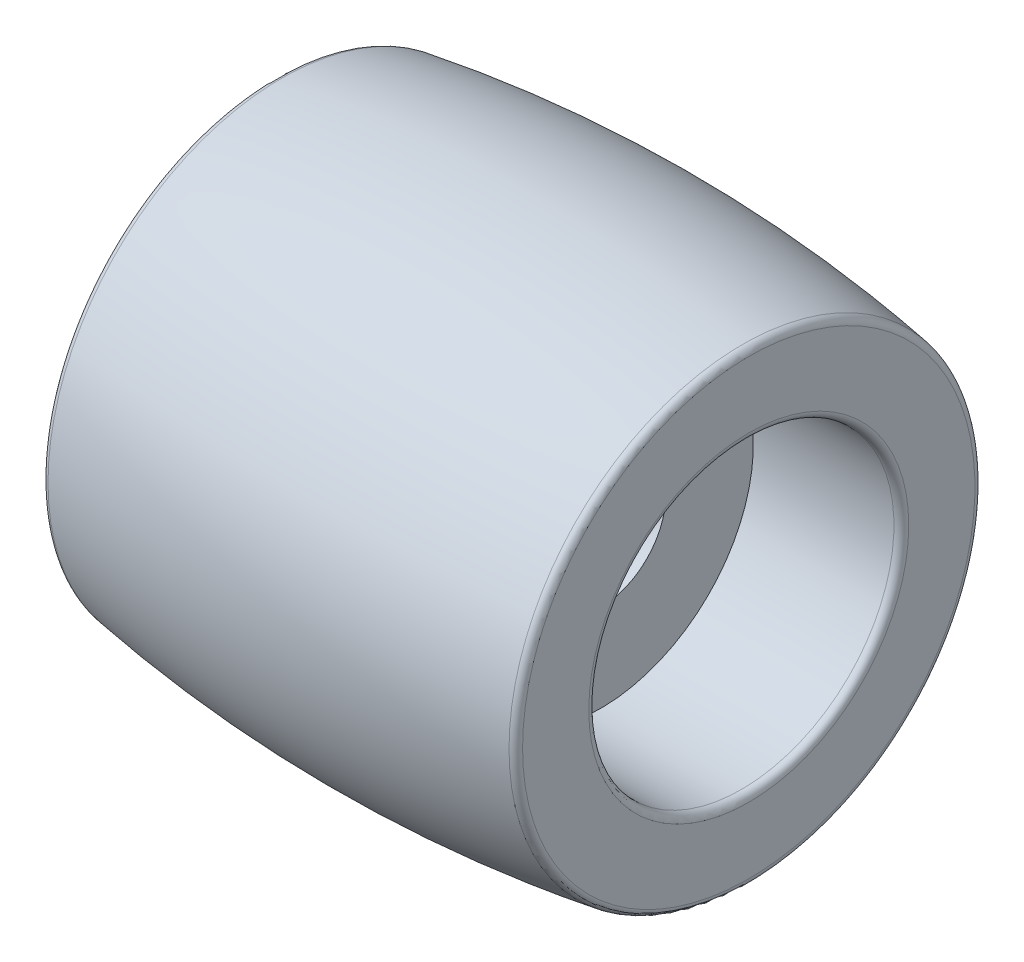
SolidWorks part; units mm, degrees
ref_plane "Front Plane" through (0, 0, 0) normal (0, 0, 1) x (1, 0, 0)
ref_plane "Top Plane" through (0, 0, 0) normal (0, 1, 0) x (1, 0, 0)
ref_plane "Right Plane" through (0, 0, 0) normal (1, 0, 0) x (0, 0, -1)
sketch "Sketch1" plane through (0, 0, 0) normal (0, 0, 1) x (1, 0, 0)
  line L0 (-9.7737, 0) -> (10.2124, 0) construction
  line L1 (-8, 7.8559) -> (-8, 5.1559)
  line L2 (-8, 5.1559) -> (-3, 5.1559)
  line L3 (-3, 5.1559) -> (-3, 2.2)
  line L4 (-3, 2.2) -> (3, 2.2)
  line L5 (3, 2.2) -> (3, 5.1559)
  line L6 (3, 5.1559) -> (8, 5.1559)
  line L7 (8, 5.1559) -> (8, 7.8559)
  arc A0 (-8, 7.8559) -> (8, 7.8559) centre (0, -41.5) cw
  point P11 (0, 2.2)
  point P13 (0, 8.5)
  dimension "D6" = 50
  dimension "D1" = 16
  dimension "D2" = 5
  dimension "D3" = 2.2
  dimension "D4" = 2.7
  dimension "D5" = 8.5
revolve "Revolve1" add sketch "Sketch1" angle 360 about L0
fillet "Fillet1" radius 0.25 4 edges at (-8, 0, 7.8559) (-8, 0, 5.1559) (8, 0, 5.1559) (8, 0, 7.8559)
